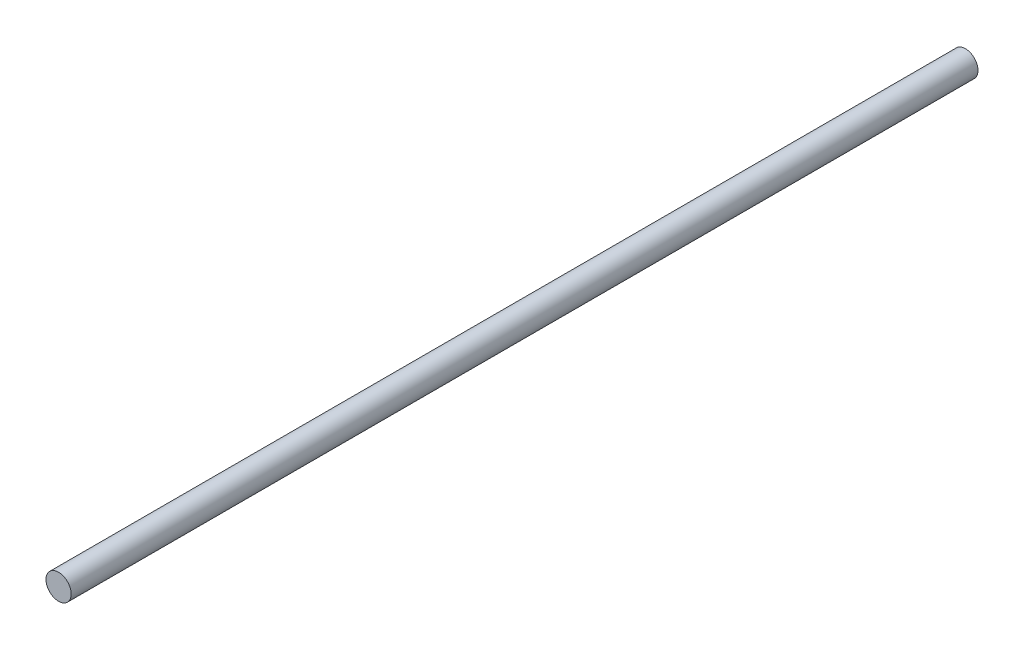
SolidWorks part; units mm, degrees
ref_plane "Front Plane" through (0, 0, 0) normal (0, 0, 1) x (1, 0, 0)
ref_plane "Top Plane" through (0, 0, 0) normal (0, 1, 0) x (1, 0, 0)
ref_plane "Right Plane" through (0, 0, 0) normal (1, 0, 0) x (0, 0, -1)
sketch "Sketch1" plane through (0, 0, 0) normal (0, 0, 1) x (1, 0, 0)
  circle A0 centre (0, 0) radius 2.5
  dimension "D1" = 5
extrude "Boss-Extrude1" add sketch "Sketch1" along normal blind 180
